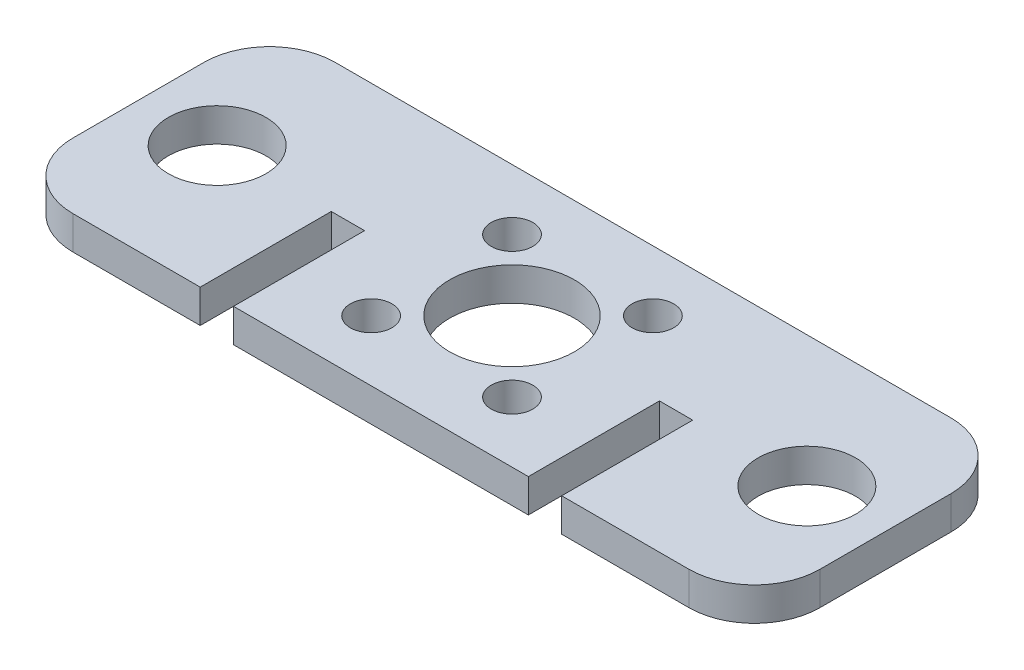
SolidWorks part; units mm, degrees
ref_plane "Front Plane" through (0, 0, 0) normal (0, 0, 1) x (1, 0, 0)
ref_plane "Top Plane" through (0, 0, 0) normal (0, 1, 0) x (1, 0, 0)
ref_plane "Right Plane" through (0, 0, 0) normal (1, 0, 0) x (0, 0, -1)
sketch "Sketch1" plane through (0, 0, 0) normal (0, 1, 0) x (1, 0, 0)
  line L0 (0, 20) -> (0, -20) construction
  line L1 (57, -20) -> (-57, -20)
  line L2 (57, -20) -> (57, 20)
  line L3 (57, 20) -> (-57, 20)
  line L4 (-57, -20) -> (-57, 20)
  line L5 (57, -20) -> (-57, 20) construction
  line L6 (57, 20) -> (-57, -20) construction
  circle A0 centre (-45, 0) radius 7.45
  circle A1 centre (45, 0) radius 7.45
  circle A2 centre (0, 0) radius 9.525
  point P0 (0, 0)
  dimension "D3" = 19.05
  dimension "D4" = 14.9
  dimension "D5" = 90
  dimension "D1" = 40
  dimension "D2" = 114
extrude "Boss-Extrude1" add sketch "Sketch1" along normal blind 5.08
fillet "Fillet1" radius 10 4 edges at (57, 2.54, -20) (57, 2.54, 20) (-57, 2.54, -20) (-57, 2.54, 20)
sketch "Sketch2" plane through (0, 5.08, 0) normal (0, 1, 0) x (1, 0, 0)
  line L0 (-47, -20) -> (47, -20) construction
  line L1 (-27.58, -20) -> (-22.5, -20)
  line L2 (-27.58, -20) -> (-27.58, 0)
  line L3 (-27.58, 0) -> (-22.5, 0)
  line L4 (-22.5, -20) -> (-22.5, 0)
  line L5 (0, 20) -> (0, -20) construction
  line L6 (27.58, -20) -> (22.5, -20)
  line L7 (27.58, -20) -> (27.58, 0)
  line L8 (27.58, 0) -> (22.5, 0)
  line L9 (22.5, -20) -> (22.5, 0)
  line L10 (47, 20) -> (-47, 20) construction
  line L12 (-10.75, -10.75) -> (10.75, -10.75) construction
  line L13 (-10.75, -10.75) -> (-10.75, 10.75) construction
  line L14 (-10.75, 10.75) -> (10.75, 10.75) construction
  line L15 (10.75, -10.75) -> (10.75, 10.75) construction
  line L16 (-10.75, -10.75) -> (10.75, 10.75) construction
  line L17 (-10.75, 10.75) -> (10.75, -10.75) construction
  circle A0 centre (10.75, -10.75) radius 3.175
  circle A1 centre (-10.75, -10.75) radius 3.175
  circle A2 centre (-10.75, 10.75) radius 3.175
  circle A3 centre (10.75, 10.75) radius 3.175
  point P14 (0, 0)
  dimension "D4" = 6.35
  dimension "D1" = 5.08
  dimension "D2" = 45
  dimension "D3" = 21.5
extrude "Cut-Extrude1" cut sketch "Sketch2" against normal through all
